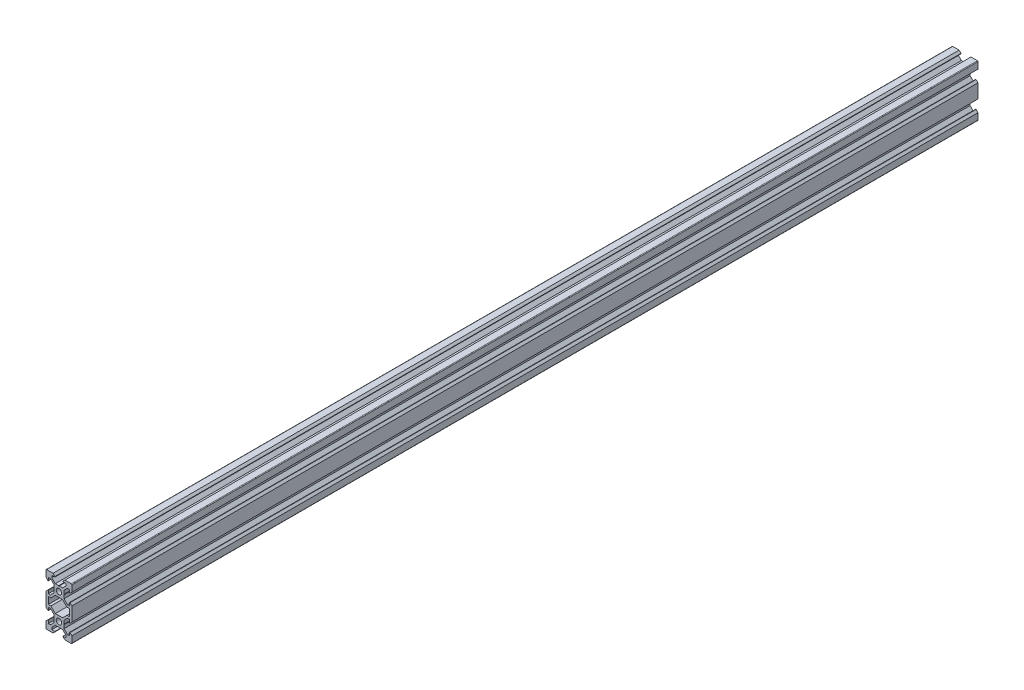
SolidWorks part; units mm, degrees
material "6061-T6 (SS)"
ref_plane "Front Plane" through (0, 0, 0) normal (0, 0, 1) x (1, 0, 0)
ref_plane "Top Plane" through (0, 0, 0) normal (0, 1, 0) x (1, 0, 0)
ref_plane "Right Plane" through (0, 0, 0) normal (1, 0, 0) x (0, 0, -1)
sketch "Sketch1" plane through (0, 0, 0) normal (0, 0, 1) x (1, 0, 0)
  line L0 (0, 0) -> (10, 0) construction
  line L1 (9.5, -20) -> (-9.5, -20)
  line L2 (10, -19.5) -> (10, 19.5)
  line L3 (9.5, 20) -> (-9.5, 20)
  line L4 (-10, -19.5) -> (-10, 19.5)
  line L5 (10, -20) -> (-10, 20) construction
  line L6 (10, 20) -> (-10, -20) construction
  circle A0 centre (0, 10) radius 2.1
  circle A1 centre (0, -10) radius 2.1
  arc A2 (-9.5, -20) -> (-10, -19.5) centre (-9.5, -19.5) cw
  arc A3 (9.5, -20) -> (10, -19.5) centre (9.5, -19.5) ccw
  arc A4 (10, 19.5) -> (9.5, 20) centre (9.5, 19.5) ccw
  arc A5 (-9.5, 20) -> (-10, 19.5) centre (-9.5, 19.5) ccw
  point P0 (0, 0)
  line B0 (0, 10) -> (0, 20) construction
  line B1 (0, 13.69) -> (-0.21, 13.9)
  line B2 (-0.21, 13.9) -> (-2.8393, 13.9)
  line B3 (-2.8393, 13.9) -> (-5.5, 16.5607)
  line B4 (-5.5, 16.5607) -> (-5.5, 18.2)
  line B5 (-5.5, 18.2) -> (-3.125, 18.2)
  line B6 (-3.125, 18.2) -> (-3.125, 18.545)
  line B7 (-3.125, 18.545) -> (-4.58, 20)
  line B8 (-4.58, 20) -> (4.58, 20)
  line B9 (0, 10) -> (-5.9132, 15.9132) construction
  line B10 (3.125, 18.545) -> (4.58, 20)
  line B11 (3.125, 18.2) -> (3.125, 18.545)
  line B12 (5.5, 18.2) -> (3.125, 18.2)
  line B13 (5.5, 16.5607) -> (5.5, 18.2)
  line B14 (2.8393, 13.9) -> (5.5, 16.5607)
  line B15 (0.21, 13.9) -> (2.8393, 13.9)
  line B16 (0, 13.69) -> (0.21, 13.9)
  line B17 (0, 10) -> (-10, 10) construction
  line B18 (-3.69, 10) -> (-3.9, 9.79)
  line B19 (-3.9, 9.79) -> (-3.9, 7.1607)
  line B20 (-3.9, 7.1607) -> (-6.5607, 4.5)
  line B21 (-6.5607, 4.5) -> (-8.2, 4.5)
  line B22 (-8.2, 4.5) -> (-8.2, 6.875)
  line B23 (-8.2, 6.875) -> (-8.545, 6.875)
  line B24 (-8.545, 6.875) -> (-10, 5.42)
  line B25 (-10, 5.42) -> (-10, 14.58)
  line B26 (0, 10) -> (-5.9132, 4.0868) construction
  line B27 (-8.545, 13.125) -> (-10, 14.58)
  line B28 (-8.2, 13.125) -> (-8.545, 13.125)
  line B29 (-8.2, 15.5) -> (-8.2, 13.125)
  line B30 (-6.5607, 15.5) -> (-8.2, 15.5)
  line B31 (-3.9, 12.8393) -> (-6.5607, 15.5)
  line B32 (-3.9, 10.21) -> (-3.9, 12.8393)
  line B33 (-3.69, 10) -> (-3.9, 10.21)
  line B34 (0, -10) -> (-10, -10) construction
  line B35 (-3.69, -10) -> (-3.9, -10.21)
  line B36 (-3.9, -10.21) -> (-3.9, -12.8393)
  line B37 (-3.9, -12.8393) -> (-6.5607, -15.5)
  line B38 (-6.5607, -15.5) -> (-8.2, -15.5)
  line B39 (-8.2, -15.5) -> (-8.2, -13.125)
  line B40 (-8.2, -13.125) -> (-8.545, -13.125)
  line B41 (-8.545, -13.125) -> (-10, -14.58)
  line B42 (-10, -14.58) -> (-10, -5.42)
  line B43 (0, -10) -> (-5.9132, -15.9132) construction
  line B44 (-8.545, -6.875) -> (-10, -5.42)
  line B45 (-8.2, -6.875) -> (-8.545, -6.875)
  line B46 (-8.2, -4.5) -> (-8.2, -6.875)
  line B47 (-6.5607, -4.5) -> (-8.2, -4.5)
  line B48 (-3.9, -7.1607) -> (-6.5607, -4.5)
  line B49 (-3.9, -9.79) -> (-3.9, -7.1607)
  line B50 (-3.69, -10) -> (-3.9, -9.79)
  line B51 (0, -10) -> (0, -20) construction
  line B52 (0, -13.69) -> (0.21, -13.9)
  line B53 (0.21, -13.9) -> (2.8393, -13.9)
  line B54 (2.8393, -13.9) -> (5.5, -16.5607)
  line B55 (5.5, -16.5607) -> (5.5, -18.2)
  line B56 (5.5, -18.2) -> (3.125, -18.2)
  line B57 (3.125, -18.2) -> (3.125, -18.545)
  line B58 (3.125, -18.545) -> (4.58, -20)
  line B59 (4.58, -20) -> (-4.58, -20)
  line B60 (0, -10) -> (5.9132, -15.9132) construction
  line B61 (-3.125, -18.545) -> (-4.58, -20)
  line B62 (-3.125, -18.2) -> (-3.125, -18.545)
  line B63 (-5.5, -18.2) -> (-3.125, -18.2)
  line B64 (-5.5, -16.5607) -> (-5.5, -18.2)
  line B65 (-2.8393, -13.9) -> (-5.5, -16.5607)
  line B66 (-0.21, -13.9) -> (-2.8393, -13.9)
  line B67 (0, -13.69) -> (-0.21, -13.9)
  line B68 (0, -10) -> (10, -10) construction
  line B69 (3.69, -10) -> (3.9, -9.79)
  line B70 (3.9, -9.79) -> (3.9, -7.1607)
  line B71 (3.9, -7.1607) -> (6.5607, -4.5)
  line B72 (6.5607, -4.5) -> (8.2, -4.5)
  line B73 (8.2, -4.5) -> (8.2, -6.875)
  line B74 (8.2, -6.875) -> (8.545, -6.875)
  line B75 (8.545, -6.875) -> (10, -5.42)
  line B76 (10, -5.42) -> (10, -14.58)
  line B77 (0, -10) -> (5.9132, -4.0868) construction
  line B78 (8.545, -13.125) -> (10, -14.58)
  line B79 (8.2, -13.125) -> (8.545, -13.125)
  line B80 (8.2, -15.5) -> (8.2, -13.125)
  line B81 (6.5607, -15.5) -> (8.2, -15.5)
  line B82 (3.9, -12.8393) -> (6.5607, -15.5)
  line B83 (3.9, -10.21) -> (3.9, -12.8393)
  line B84 (3.69, -10) -> (3.9, -10.21)
  line B85 (0, 10) -> (10, 10) construction
  line B86 (3.69, 10) -> (3.9, 10.21)
  line B87 (3.9, 10.21) -> (3.9, 12.8393)
  line B88 (3.9, 12.8393) -> (6.5607, 15.5)
  line B89 (6.5607, 15.5) -> (8.2, 15.5)
  line B90 (8.2, 15.5) -> (8.2, 13.125)
  line B91 (8.2, 13.125) -> (8.545, 13.125)
  line B92 (8.545, 13.125) -> (10, 14.58)
  line B93 (10, 14.58) -> (10, 5.42)
  line B94 (0, 10) -> (5.9132, 15.9132) construction
  line B95 (8.545, 6.875) -> (10, 5.42)
  line B96 (8.2, 6.875) -> (8.545, 6.875)
  line B97 (8.2, 4.5) -> (8.2, 6.875)
  line B98 (6.5607, 4.5) -> (8.2, 4.5)
  line B99 (3.9, 7.1607) -> (6.5607, 4.5)
  line B100 (3.9, 9.79) -> (3.9, 7.1607)
  line B101 (3.69, 10) -> (3.9, 9.79)
  line B102 (-8.2, -2.7) -> (-8.2, 2.7)
  line B103 (-8.2, 2.7) -> (-6.2393, 2.7)
  line B104 (-6.2393, 2.7) -> (-2.8393, 6.1)
  line B105 (-2.8393, 6.1) -> (2.8393, 6.1)
  line B106 (0, 6.1) -> (0, 0) construction
  line B107 (0, 0) -> (-8.2, 0) construction
  line B108 (6.2393, 2.7) -> (2.8393, 6.1)
  line B109 (8.2, 2.7) -> (6.2393, 2.7)
  line B110 (8.2, -2.7) -> (8.2, 2.7)
  line B111 (8.2, -2.7) -> (6.2393, -2.7)
  line B112 (6.2393, -2.7) -> (2.8393, -6.1)
  line B113 (-2.8393, -6.1) -> (2.8393, -6.1)
  line B114 (-6.2393, -2.7) -> (-2.8393, -6.1)
  line B115 (-8.2, -2.7) -> (-6.2393, -2.7)
  line B116 (0, 6.1) -> (0, 10) construction
  line B117 (0, 10) -> (-5.0927, 4.9073) construction
sketch_block_instance "V Slot 1-4"
sketch_block "V Slot 1" parameters "D1"=10, "D2"=11, "D3"=4.3, "D4"=1.8, "D5"=0.21, "D6"=45, "D7"=9.16, "D8"=1.5, "D9"=6.25
sketch_block_instance "V Slot 1-5"
sketch_block_instance "V Slot 1-6"
sketch_block_instance "V Slot 1-7"
sketch_block_instance "V Slot 1-8"
sketch_block_instance "V Slot 1-9"
sketch_block_instance "Center Cutout 1-1"
sketch_block "Center Cutout 1" parameters "D1"=5.4, "D2"=12.2, "D3"=8.2, "D4"=45, "D5"=10, "D6"=1.5
extrude "Boss-Extrude1" add sketch "Sketch1" along normal blind 700 contours B101 B86 B87 B88 B89 B90 B91 B92 L2 A4 L3 B10 B11 B12 B13 B14 B15 B16 B1 B2 B3 B4 B5 B6 B7 A5 L4 B27 B28 B29 B30 B31 B32 B33 B18 B19 B20 B21 B22 B23 B24 B44 B45 B46 B47 B48 B49 B50 B35
